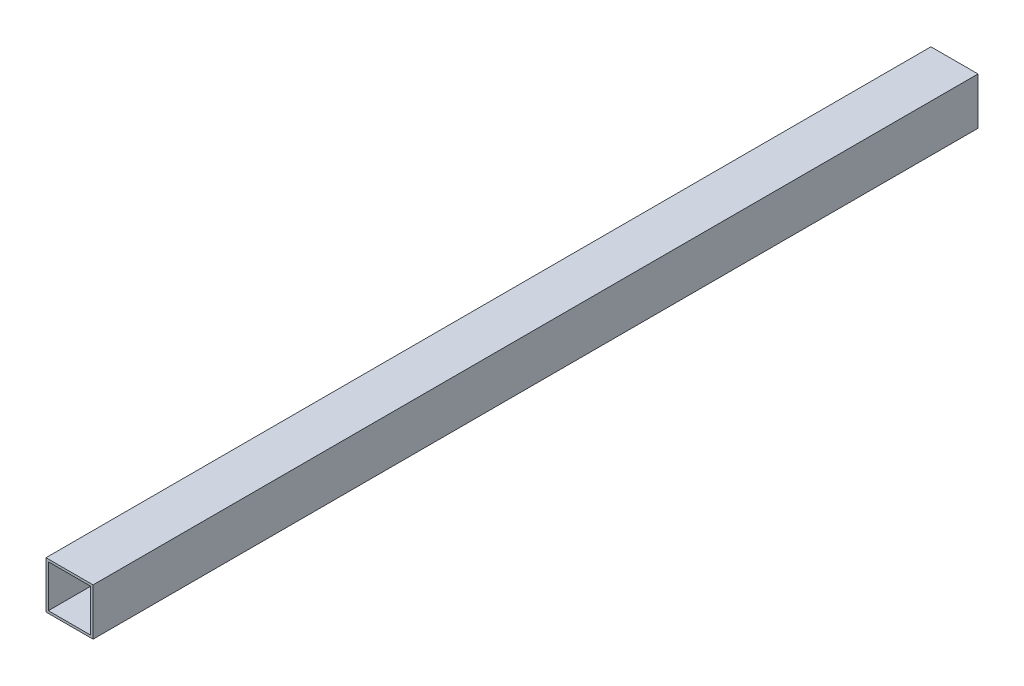
SolidWorks part; units mm, degrees
material "Plain Carbon Steel"
ref_plane "Front Plane" through (0, 0, 0) normal (0, 0, 1) x (1, 0, 0)
ref_plane "Top Plane" through (0, 0, 0) normal (0, 1, 0) x (1, 0, 0)
ref_plane "Right Plane" through (0, 0, 0) normal (1, 0, 0) x (0, 0, -1)
sketch "Sketch1" plane through (0, 0, 0) normal (0, 0, 1) x (1, 0, 0)
  line B0 (-50, -50) -> (50, -50)
  line B1 (-50, -50) -> (-50, 50)
  line B2 (50, -50) -> (50, 50)
  line B3 (-50, 50) -> (50, 50)
  line B4 (-45, -45) -> (45, -45)
  line B5 (-45, -45) -> (-45, 45)
  line B6 (45, -45) -> (45, 45)
  line B7 (-45, 45) -> (45, 45)
sketch_block_instance "10x10x5_profil-1"
sketch_block "10x10x5_profil" parameters "D1"=100, "D2"=100, "D3"=5, "D4"=5
extrude "Boss-Extrude1" add sketch "Sketch1" along normal mid plane 1880
